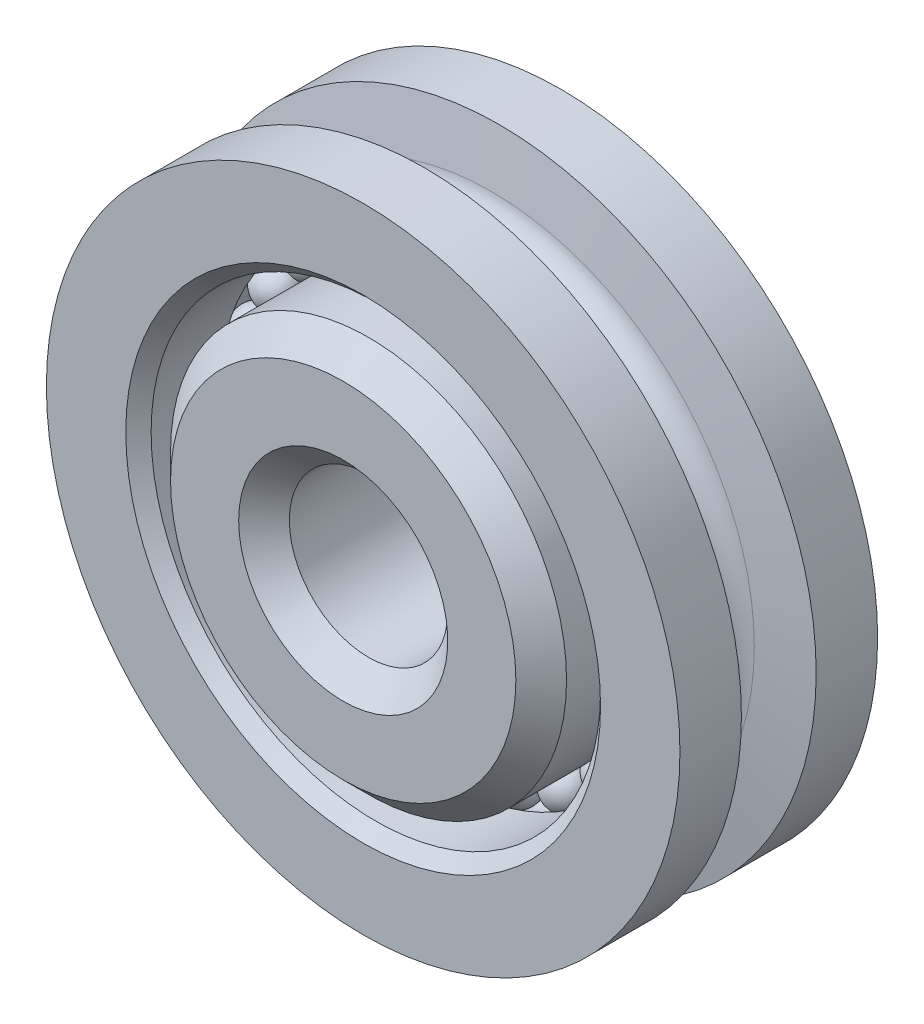
SolidWorks part; units mm, degrees
material "A-Glass Fiber"
ref_plane "Front" through (0, 0, 0) normal (0, 0, 1) x (1, 0, 0)
ref_plane "Top" through (0, 0, 0) normal (0, 1, 0) x (1, 0, 0)
ref_plane "Right" through (0, 0, 0) normal (1, 0, 0) x (0, 0, -1)
sketch "Sketch1" plane through (0, 0, 0) normal (1, 0, 0) x (0, 0, -1)
  line L0 (0.7493, 6.35) -> (1.9812, 6.35)
  line L1 (-0.7493, 6.35) -> (-1.9812, 6.35)
  line L2 (-0.7493, 6.35) -> (-0.5888, 5.2703)
  line L3 (0.3572, 4.5045) -> (1.9812, 4.5045)
  line L4 (2.3812, 1.5875) -> (-2.3812, 1.5875)
  line L5 (-0.3572, 3.9688) -> (-2.3813, 3.9688)
  line L6 (0.7493, 6.35) -> (0.5888, 5.2703)
  line L8 (-2.3812, 0) -> (2.3812, 0) construction
  line L10 (1.9812, 6.35) -> (1.9812, 4.5045)
  line L13 (-2.3813, 3.9688) -> (-2.3812, 1.5875)
  line L14 (0, 4.7625) -> (0, -4.7625) construction
  line L16 (2.3813, 3.9688) -> (2.3812, 1.5875)
  line L17 (-1.9812, 6.35) -> (-1.9812, -6.35) construction
  line L18 (-1.9812, 4.5045) -> (-0.3572, 4.5045)
  line L20 (2.3813, 3.9688) -> (0.3572, 3.9688)
  line L21 (-1.9812, 4.5045) -> (-1.9812, 6.35)
  arc A0 (-0.5888, 5.2703) -> (0.5888, 5.2703) centre (0, 5.3578) ccw
  circle A1 centre (0, 5.3578) radius 0.5953 construction
  circle A2 centre (0, 0) radius 1.5875 construction
  circle A3 centre (0, 0) radius 3.9688 construction
  arc A4 (-0.3572, 3.9688) -> (0.3572, 3.9688) centre (0, 4.2366) ccw
  circle A5 centre (0, -5.3578) radius 0.5953 construction
  arc A6 (0.3572, 4.5045) -> (-0.3572, 4.5045) centre (0, 4.2366) ccw
  point P28 (-1.9812, 0)
  dimension "Rope Dia" = 1.1906
  dimension "Shaft Dia" = 3.175
  dimension "D1" = 7.9375
  dimension "D2" = 0.893
  dimension "Wd" = 4.7625
  dimension "D8" = 1.2319
  dimension "Groove Dia" = 9.525
  dimension "OD" = 12.7
  dimension "w Wd" = 3.9624
  dimension "D3" = 0.5358
revolve "Revolve1" add sketch "Sketch1" angle 360 about L8
sketch "Sketch2" plane through (0, 0, 0) normal (1, 0, 0) x (0, 0, -1)
  line L0 (0, 4.7625) -> (0, -4.7625) construction
  line L1 (0, 4.6831) -> (0, 3.7902)
  arc A0 (0.3572, 4.5045) -> (-0.3572, 4.5045) centre (0, 4.2366) ccw construction
  arc A1 (0, 3.7902) -> (0, 4.6831) centre (0, 4.2366) ccw
revolve "Revolve2" add sketch "Sketch2" angle 360 about L1
pattern_circular "CirPattern1" count 24 over 360 about axis through (0, 0, 0) along (0, 0, 1) of bodies 117
chamfer "Chamfer1" distance 0.508 angle 45 4 edges at (1.5875, 0, -2.3812) (3.9688, 0, -2.3813) (3.9688, 0, 2.3813) (1.5875, 0, 2.3812)
chamfer "Chamfer2" distance 0.254 angle 45 2 edges at (4.5045, 0, -1.9812) (4.5045, 0, 1.9812)
equation "\"D1@Sketch1\" = \"Shaft Dia@Sketch1\" * 2.5"
equation "\"D2@Sketch1\" = \"Rope Dia@Sketch1\" * .75"
equation "\"D3@Sketch1\" = \"D2@Sketch1\" * .6"
